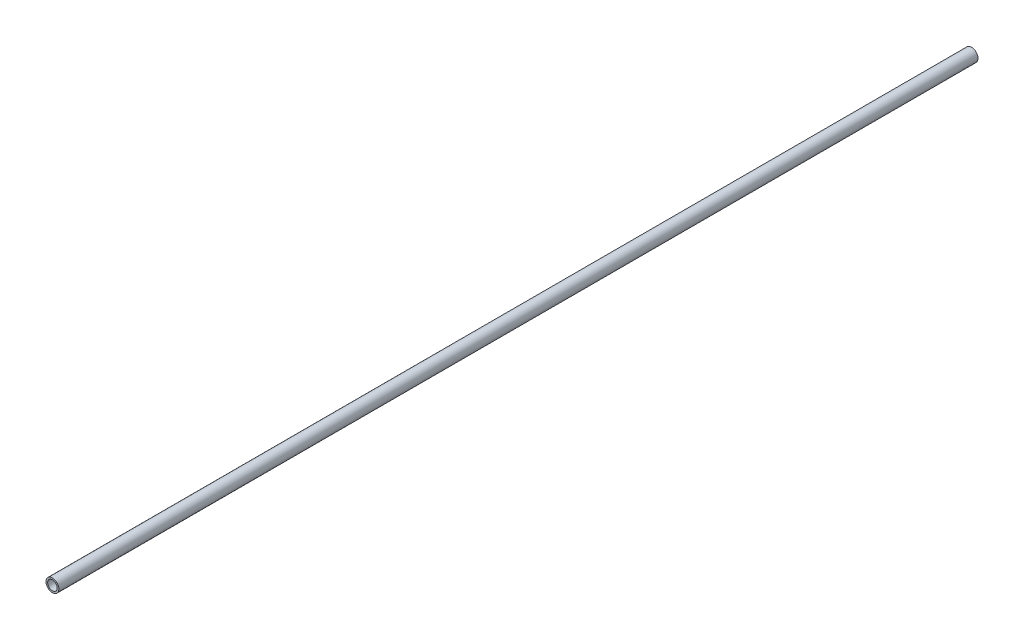
SolidWorks part; units mm, degrees
material "6061 Alloy"
ref_plane "Front Plane" through (0, 0, 0) normal (0, 0, 1) x (1, 0, 0)
ref_plane "Top Plane" through (0, 0, 0) normal (0, 1, 0) x (1, 0, 0)
ref_plane "Right Plane" through (0, 0, 0) normal (1, 0, 0) x (0, 0, -1)
sketch "Sketch1" plane through (0, 0, 0) normal (0, 0, 1) x (1, 0, 0)
  circle A0 centre (0, 0) radius 7.8994
  circle A1 centre (0, 0) radius 10.668
  dimension "D1" = 21.336
  dimension "D2" = 15.7988
extrude "Boss-Extrude1" add sketch "Sketch1" along normal blind 1524
